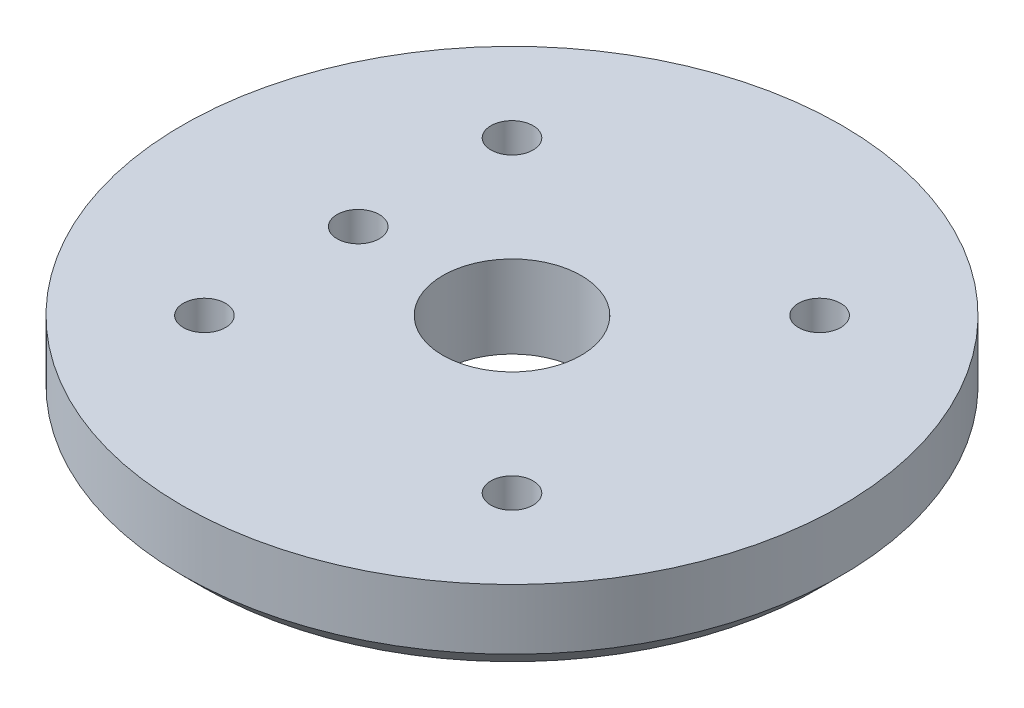
SolidWorks part; units mm, degrees
material "ABS PLASTIC"
ref_plane "Front Plane" through (0, 0, 0) normal (0, 0, 1) x (1, 0, 0)
ref_plane "Top Plane" through (0, 0, 0) normal (0, 1, 0) x (1, 0, 0)
ref_plane "Right Plane" through (0, 0, 0) normal (1, 0, 0) x (0, 0, -1)
sketch "Sketch1" plane through (0, 0, 0) normal (0, 1, 0) x (1, 0, 0)
  circle A0 centre (0, 0) radius 19.05
  circle A1 centre (0, 0) radius 4
  dimension "D1" = 38.1
  dimension "D2" = 8
extrude "Boss-Extrude1" add sketch "Sketch1" along normal blind 4.7625
hole_wizard "#2 Clearance Hole1" positions "Sketch3" profile "Sketch4" hole size "#2" standard "ANSI Inch" end condition up to next
sketch "Sketch3" plane through (0, 4.7625, 0) normal (0, 1, 0) x (1, 0, 0)
  line L1 (-8.89, -8.89) -> (8.89, -8.89)
  line L2 (-8.89, -8.89) -> (-8.89, 8.89)
  line L3 (-8.89, 8.89) -> (8.89, 8.89)
  line L4 (8.89, -8.89) -> (8.89, 8.89)
  line L5 (-8.89, -8.89) -> (8.89, 8.89) construction
  line L6 (-8.89, 8.89) -> (8.89, -8.89) construction
  point P0 (-8.89, 8.89)
  point P2 (8.89, 8.89)
  point P4 (-8.89, -8.89)
  point P6 (8.89, -8.89)
  point P38 (0, 8.89)
  point P46 (-8.89, 0)
  dimension "D1" = 17.78
sketch "Sketch4" plane through (-8.89, 4.7625, -8.89) normal (1, 0, 0) x (0, 0, 1)
  line L0 (0, 0) -> (0, 4.7625)
  line L1 (0, 4.7625) -> (1.2192, 4.7625)
  line L2 (1.2192, 4.7625) -> (1.2192, 0)
  line L5 (1.2192, 0) -> (0, 0)
  line L11 (0, -6.35) -> (0, 107.95) construction
  dimension "Thru Hole Dia." = 2.4384
  dimension "Thru Hole Depth" = 4.7625
chamfer "Chamfer1" distance 1.27 angle 45 1 edges at (0, 0, 19.05)
